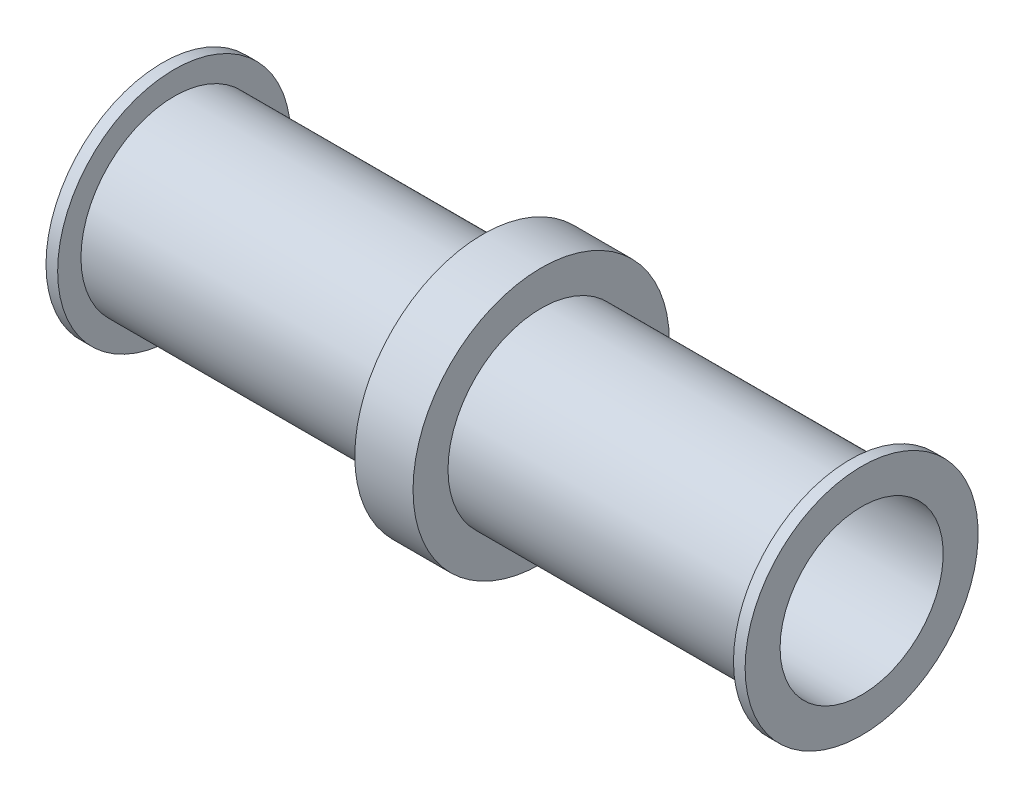
SolidWorks part; units mm, degrees
material "PVC Rigid"
ref_plane "Front Plane" through (0, 0, 0) normal (0, 0, 1) x (1, 0, 0)
ref_plane "Top Plane" through (0, 0, 0) normal (0, 1, 0) x (1, 0, 0)
ref_plane "Right Plane" through (0, 0, 0) normal (1, 0, 0) x (0, 0, -1)
sketch "Sketch1" plane through (0, 0, 0) normal (0, 0, 1) x (1, 0, 0)
  line L0 (0, 0) -> (87.134, 0) construction
  line L1 (0, 1.778) -> (0, 2.54)
  line L2 (0, 2.54) -> (0.254, 2.54)
  line L3 (0.254, 2.54) -> (0.254, 2.032)
  line L4 (0.254, 2.032) -> (6.985, 2.032)
  line L5 (8.255, 2.032) -> (8.255, 2.794)
  line L6 (8.255, 2.794) -> (6.985, 2.794)
  line L7 (6.985, 2.794) -> (6.985, 2.032)
  line L8 (8.255, 2.032) -> (14.986, 2.032)
  line L9 (14.986, 2.032) -> (14.986, 2.54)
  line L10 (14.986, 2.54) -> (15.24, 2.54)
  line L11 (15.24, 2.54) -> (15.24, 1.778)
  line L14 (0, 1.778) -> (15.24, 1.778)
  line L17 (7.62, 0) -> (7.62, 21.522) construction
  dimension "D1" = 7.62
  dimension "D2" = 0.254
  dimension "D3" = 1.27
  dimension "D4" = 15.24
  dimension "D5" = 0.254
  dimension "D6" = 2.794
  dimension "D7" = 1.778
  dimension "D8" = 2.54
revolve "Revolve1" add sketch "Sketch1" angle 360 about L0
